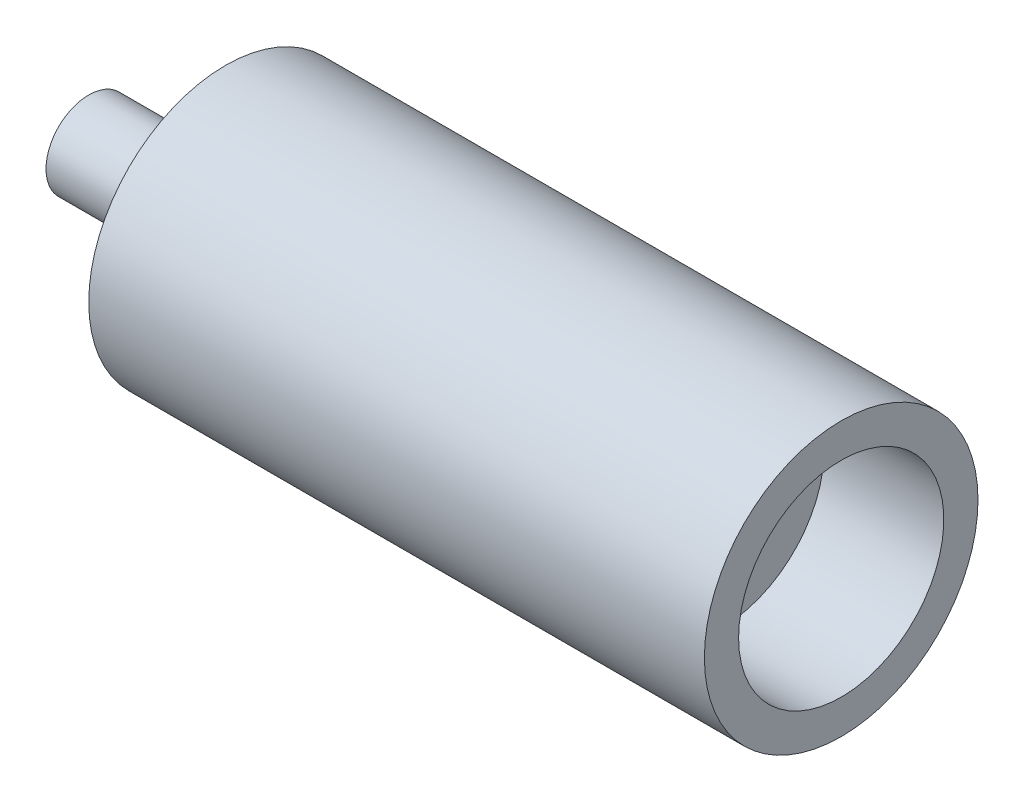
SolidWorks part; units mm, degrees
material "6061-T6 (SS)"
ref_plane "Front Plane" through (0, 0, 0) normal (0, 0, 1) x (1, 0, 0)
ref_plane "Top Plane" through (0, 0, 0) normal (0, 1, 0) x (1, 0, 0)
ref_plane "Right Plane" through (0, 0, 0) normal (1, 0, 0) x (0, 0, -1)
sketch "Sketch1" plane through (0, 0, 0) normal (0, 0, 1) x (1, 0, 0)
  line L0 (0, 6.35) -> (0, 12.5)
  line L1 (0, 12.5) -> (30, 12.5)
  line L2 (30, 12.5) -> (30, 20)
  line L3 (30, 20) -> (33, 25)
  line L4 (33, 25) -> (35, 25)
  line L5 (35, 25) -> (35, 32.5)
  line L6 (35, 32.5) -> (40, 32.5)
  line L7 (40, 32.5) -> (40, 40)
  line L8 (40, 40) -> (220, 40)
  line L9 (220, 40) -> (220, 30)
  line L10 (220, 30) -> (185, 30)
  line L11 (185, 30) -> (185, 5)
  line L13 (1.425, 0) -> (39.9893, 0) construction
  line L14 (0, 6.35) -> (50, 6.35)
  line L15 (50, 6.35) -> (50, 5)
  line L16 (50, 5) -> (185, 5)
  dimension "D1" = 30
  dimension "D2" = 25
  dimension "D3" = 12.7
  dimension "D4" = 50
  dimension "D5" = 2
  dimension "D6" = 5
  dimension "D7" = 180
  dimension "D8" = 35
  dimension "D9" = 10
  dimension "D10" = 80
  dimension "D11" = 35
  dimension "D12" = 10
  dimension "D13" = 50
  dimension "D14" = 65
  dimension "D15" = 40
revolve "Revolve1" add sketch "Sketch1" angle 360 about L13
